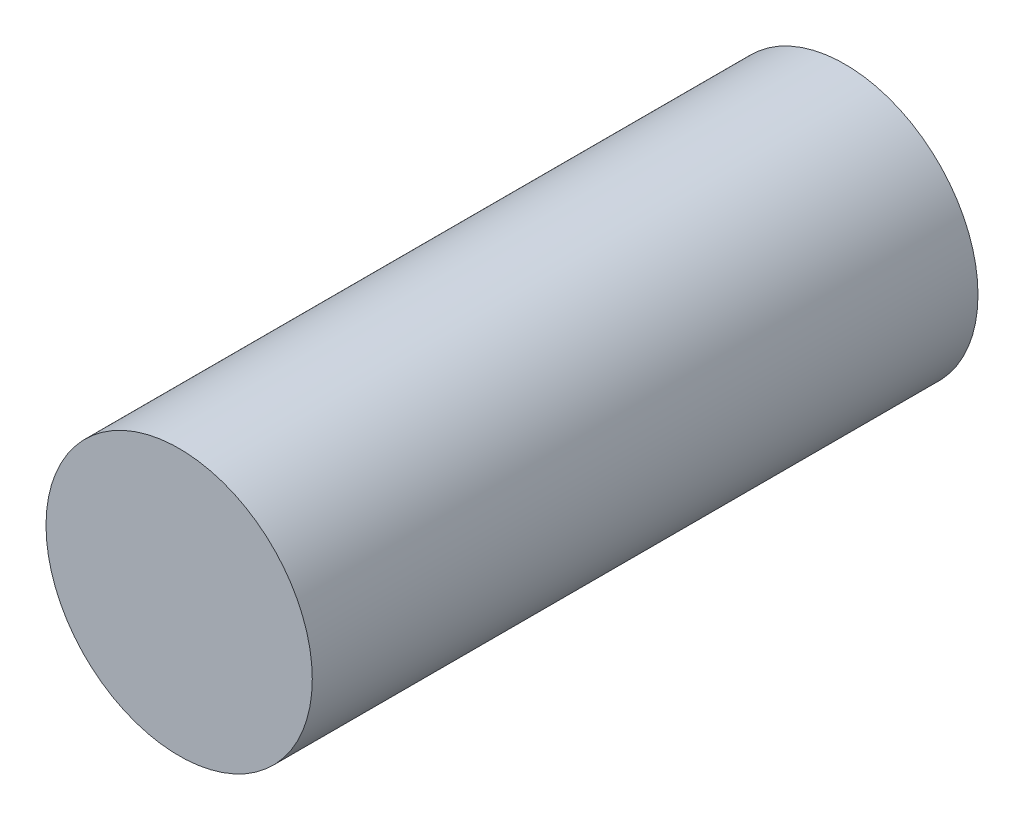
SolidWorks part; units mm, degrees
ref_plane "Front" through (0, 0, 0) normal (0, 0, 1) x (1, 0, 0)
ref_plane "Top" through (0, 0, 0) normal (0, 1, 0) x (1, 0, 0)
ref_plane "Right" through (0, 0, 0) normal (1, 0, 0) x (0, 0, -1)
sketch "Esquisse1" plane through (0, 0, 0) normal (0, 0, 1) x (1, 0, 0)
  circle A0 centre (0, 0) radius 4
  dimension "D1" = 8
extrude "Boss.-Extru.1" add sketch "Esquisse1" along normal blind 20
sketch "Esquisse2" plane through (0, 0, 0) normal (0, 0, -1) x (-1, 0, 0)
  circle A0 centre (0, 0) radius 1.75
  dimension "D1" = 3.5
extrude "Enlèv. mat.-Extru.1" cut sketch "Esquisse2" against normal blind 10
sketch "Esquisse3" plane through (0, 0, 0) normal (0, 0, -1) x (-1, 0, 0)
  circle A0 centre (0, 0) radius 2
  dimension "D1" = 4
extrude "Enlèv. mat.-Extru.2" cut sketch "Esquisse3" against normal blind 5
